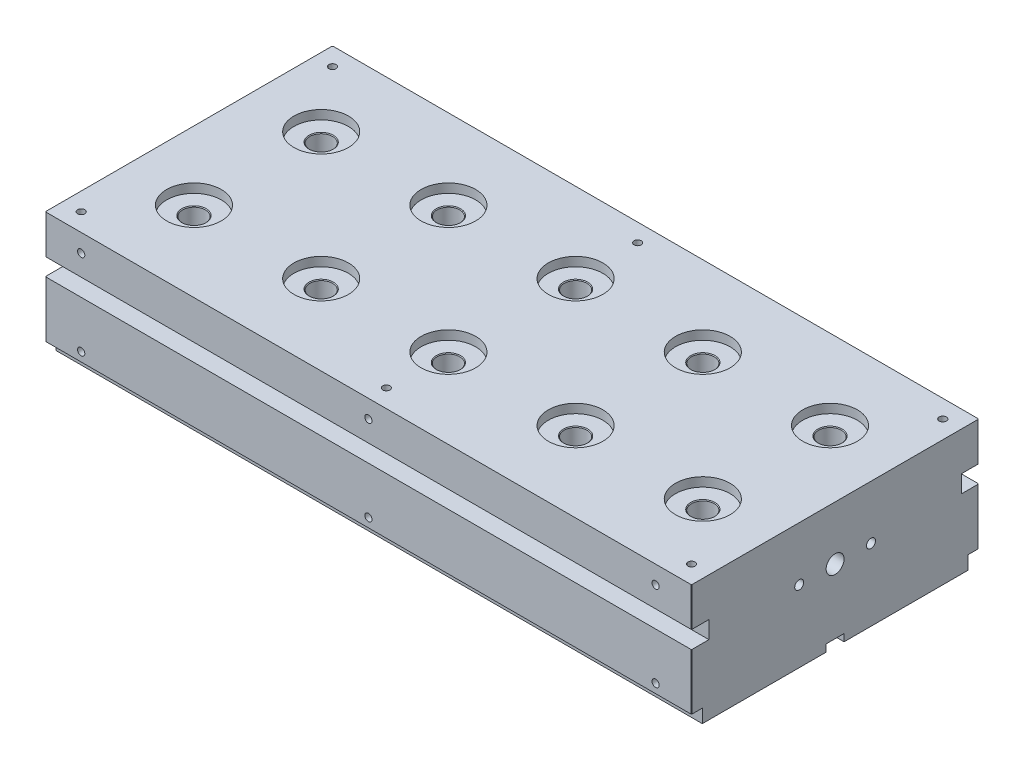
SolidWorks part; units mm, degrees
ref_plane "Front Plane" through (0, 0, 0) normal (0, 0, 1) x (1, 0, 0)
ref_plane "Top Plane" through (0, 0, 0) normal (0, 1, 0) x (1, 0, 0)
ref_plane "Right Plane" through (0, 0, 0) normal (1, 0, 0) x (0, 0, -1)
sketch "Sketch2" plane through (0, 0, 0) normal (0, 1, 0) x (1, 0, 0)
  line L1 (228.6, 101.6) -> (-228.6, 101.6)
  line L2 (228.6, 101.6) -> (228.6, -101.6)
  line L3 (228.6, -101.6) -> (-228.6, -101.6)
  line L4 (-228.6, 101.6) -> (-228.6, -101.6)
  line L5 (0, -101.6) -> (0, 101.6) construction
  line L6 (228.6, 0) -> (-228.6, 0) construction
  point P0 (0, 0)
  dimension "D1" = 457.2
  dimension "D2" = 203.2
extrude "Boss-Extrude1" add sketch "Sketch2" against normal blind 101.6
sketch "Sketch3" plane through (0, 0, 0) normal (0, 1, 0) x (1, 0, 0)
  line L0 (-90, 45) -> (-90, -45) construction
  line L1 (180, 45) -> (-180, 45) construction
  line L2 (180, 45) -> (180, -45) construction
  line L3 (180, -45) -> (-180, -45) construction
  line L4 (-180, 45) -> (-180, -45) construction
  line L5 (0, -45) -> (0, 45) construction
  line L6 (180, 0) -> (-180, 0) construction
  line L7 (90, -45) -> (90, 45) construction
  point P0 (0, 0)
  dimension "D1" = 90
  dimension "D2" = 360
  dimension "D3" = 90
  dimension "D4" = 90
hole_wizard "#97 (0.0059) Diameter Hole1" positions "Sketch4" profile "Sketch5" hole size "#97" standard "ANSI Inch" end condition up to next
sketch "Sketch4" plane through (0, 0, 0) normal (0, 1, 0) x (1, 0, 0)
  point P0 (-180, 45)
  point P3 (-180, -45)
  point P6 (-90, -45)
  point P9 (-90, 45)
  point P12 (0, 45)
  point P15 (0, -45)
  point P18 (90, 45)
  point P21 (90, -45)
  point P24 (180, 45)
  point P27 (180, -45)
sketch "Sketch5" plane through (-180, 0, -45) normal (1, 0, 0) x (0, 0, 1)
  line L0 (0, 0) -> (0, 101.6)
  line L1 (0, 101.6) -> (8.0645, 101.6)
  line L2 (8.0645, 101.6) -> (8.0645, 0)
  line L5 (8.0645, 0) -> (0, 0)
  line L11 (0, -6.35) -> (0, 107.95) construction
  dimension "Thru Hole Dia." = 16.129
  dimension "Thru Hole Depth" = 101.6
sketch "Sketch6" plane through (0, 0, 0) normal (0, 1, 0) x (1, 0, 0)
  circle A0 centre (-180, 45) radius 19.304
  circle A1 centre (-90, 45) radius 19.304
  circle A2 centre (0, 45) radius 19.304
  circle A3 centre (90, 45) radius 19.304
  circle A4 centre (180, 45) radius 19.304
  circle A5 centre (-180, -45) radius 19.304
  circle A6 centre (-90, -45) radius 19.304
  circle A7 centre (0, -45) radius 19.304
  circle A8 centre (90, -45) radius 19.304
  circle A9 centre (180, -45) radius 19.304
  dimension "D1" = 38.608
extrude "Cut-Extrude1" cut sketch "Sketch6" against normal offset from surface (19.1 mm away) 82.5 up to face at (-180, -101.6, -53.0645)
sketch "Sketch7" plane through (228.6, 0, 0) normal (1, 0, 0) x (0, 0, -1)
  line L0 (0, 0) -> (0, -101.6) construction
  line L1 (-101.6, -101.6) -> (101.6, -101.6) construction
  circle A0 centre (0, -50.8) radius 6.35
  dimension "D1" = 12.7
extrude "Cut-Extrude2" cut sketch "Sketch7" against normal through all
sketch "Sketch9" plane through (228.6, 0, 0) normal (1, 0, 0) x (0, 0, -1)
  line L0 (-125.6316, -92.075) -> (-93.96, -92.075)
  line L1 (-93.96, -92.075) -> (-93.96, -105.6328)
  line L2 (-93.96, -105.6328) -> (93.96, -105.6328)
  line L3 (93.96, -105.6328) -> (93.96, -92.075)
  line L4 (93.96, -92.075) -> (107.4884, -92.075)
  line L5 (107.4884, -92.075) -> (107.4884, -145.3143)
  line L6 (107.4884, -145.3143) -> (-125.6316, -145.3143)
  line L7 (-125.6316, -145.3143) -> (-125.6316, -92.075)
  line L8 (-101.6, -101.6) -> (101.6, -101.6) construction
  point P3 (0, -105.6328)
  dimension "D1" = 187.92
  dimension "D2" = 9.525
extrude "Cut-Extrude3" cut sketch "Sketch9" against normal through all
sketch "Sketch10" plane through (0, 0, 93.96) normal (0, 0, 1) x (1, 0, 0)
  line L0 (-228.6, -96.8375) -> (228.6, -96.8375) construction
  line L1 (-228.6, -101.6) -> (-228.6, -92.075) construction
  line L2 (228.6, -101.6) -> (228.6, -92.075) construction
  point P6 (-71.12, -96.8375)
  point P7 (71.12, -96.8375)
  point P8 (-213.36, -96.8375)
  point P9 (213.36, -96.8375)
  dimension "D1" = 71.12
  dimension "D2" = 71.12
  dimension "D3" = 142.24
  dimension "D4" = 142.24
hole_wizard "#4-40 Tapped Hole1" positions "Sketch11" profile "Sketch12" tap size "#4-40" standard "ANSI Inch"
sketch "Sketch11" plane through (0, 0, 93.96) normal (0, 0, 1) x (1, 0, 0)
  point P0 (-213.36, -96.8375)
  point P3 (-71.12, -96.8375)
  point P6 (71.12, -96.8375)
  point P9 (213.36, -96.8375)
sketch "Sketch12" plane through (-213.36, -96.8375, 93.96) normal (1, 0, 0) x (0, -1, 0)
  line L0 (0, 0) -> (0, 9.5692)
  line L1 (0, 9.5692) -> (1.1303, 8.89)
  line L2 (1.1303, 8.89) -> (1.1303, 0.5461)
  line L3 (1.1303, 0.5461) -> (1.6764, 0)
  line L5 (1.6764, 0) -> (0, 0)
  line L6 (-1.1303, 0.5461) -> (-1.6764, 0) construction
  line L10 (0, 9.5692) -> (-1.1303, 8.89) construction
  line L11 (0, -6.35) -> (0, 107.95) construction
  dimension "Tap Drill Dia." = 2.2606
  dimension "Tap Drill Depth" = 8.89
  dimension "Near C'Sink Dia." = 3.3528
  dimension "Near C'Sink Angle" = 90
  dimension "Drill Angle" = 118
cosmetic thread "Hole Thread1" parameters "D1"=5.588, "D2"=2.8448
cosmetic thread "Hole Thread2" parameters "D1"=5.588, "D2"=2.8448
cosmetic thread "Hole Thread3" parameters "D1"=5.588, "D2"=2.8448
cosmetic thread "Hole Thread4" parameters "D1"=5.588, "D2"=2.8448
mirror "Mirror1" about plane through (0, 0, 0) normal (0, 0, 1) of "#4-40 Tapped Hole1"
sketch "Sketch13" plane through (0, -101.6, 0) normal (0, -1, 0) x (1, 0, 0)
  line L0 (238.321, 6.35) -> (-258.7863, 6.35)
  line L1 (-258.7863, -6.35) -> (238.321, -6.35)
  line L2 (238.321, -6.35) -> (238.321, 6.35)
  line L3 (-258.7863, 6.35) -> (-258.7863, -6.35)
  line L4 (-228.6, 0) -> (228.6, 0) construction
  point P2 (238.321, 0)
  dimension "D1" = 12.7
extrude "Cut-Extrude4" cut sketch "Sketch13" against normal blind 5.08
hole_wizard "#10-32 Tapped Hole1" positions "Sketch16" profile "Sketch15" tap size "#10-32" standard "ANSI Inch"
sketch "Sketch16" plane through (0, -96.52, 0) normal (0, -1, 0) x (-1, 0, 0)
  point P0 (0, 0)
sketch "Sketch15" plane through (0, -96.52, 0) normal (1, 0, 0) x (0, 0, -1)
  line L0 (0, 0) -> (0, 14.9293)
  line L1 (0, 14.9293) -> (2.0193, 13.716)
  line L2 (2.0193, 13.716) -> (2.0193, 0.6096)
  line L3 (2.0193, 0.6096) -> (2.6289, 0)
  line L5 (2.6289, 0) -> (0, 0)
  line L6 (-2.0193, 0.6096) -> (-2.6289, 0) construction
  line L10 (0, 14.9293) -> (-2.0193, 13.716) construction
  line L11 (0, -6.35) -> (0, 107.95) construction
  dimension "Tap Drill Dia." = 4.0386
  dimension "Tap Drill Depth" = 13.716
  dimension "Near C'Sink Dia." = 5.2578
  dimension "Near C'Sink Angle" = 90
  dimension "Drill Angle" = 118
cosmetic thread "Hole Thread5" parameters "D1"=9.652, "D2"=4.826
chamfer "Chamfer1" distance 0.508 angle 45 28 edges at (180, 0, -25.696) (180, 0, 64.304) (90, 0, -25.696) (90, 0, 64.304) (0, 0, 64.304) (0, 0, -25.696) (-90, 0, -25.696) (-90, 0, 64.304) (-180, 0, 64.304) (-180, 0, -25.696) (-180, -19.1, -53.0645) (-180, -19.1, 36.9355) (-90, -19.1, 36.9355) (-90, -19.1, -53.0645) (0, -19.1, -53.0645) (0, -19.1, 36.9355) (90, -19.1, -53.0645) (90, -19.1, 36.9355) (180, -19.1, 36.9355) (180, -19.1, -53.0645) (0, 0, -101.6) (228.6, -46.0375, -101.6) (228.6, 0, 0) (228.6, -46.0375, 101.6) (0, 0, 101.6) (-228.6, -46.0375, -101.6) (-228.6, 0, 0) (-228.6, -46.0375, 101.6)
sketch "Sketch17" plane through (-228.6, 0, 0) normal (-1, 0, 0) x (0, 0, 1)
  line L0 (-127.8007, -12.7) -> (122.3798, -12.7)
  line L1 (122.3798, -12.7) -> (122.3798, -40.132)
  line L2 (122.3798, -40.132) -> (89.281, -40.132)
  line L3 (89.281, -40.132) -> (89.281, -52.451)
  line L4 (89.281, -52.451) -> (139.4159, -52.451)
  line L5 (139.4159, -52.451) -> (139.4159, 38.5706)
  line L6 (139.4159, 38.5706) -> (-149.881, 38.5706)
  line L7 (-149.881, 38.5706) -> (-149.881, -52.451)
  line L8 (-149.881, -52.451) -> (-89.281, -52.451)
  line L9 (-89.281, -52.451) -> (-89.281, -40.132)
  line L10 (-89.281, -40.132) -> (-127.8007, -40.132)
  line L11 (-127.8007, -40.132) -> (-127.8007, -12.7)
  line L12 (-101.092, 0) -> (101.092, 0) construction
  line L13 (101.6, -0.508) -> (101.6, -92.075) construction
  line L14 (-101.6, -92.075) -> (-101.6, -0.508) construction
  dimension "D1" = 12.7
  dimension "D2" = 12.319
  dimension "D3" = 12.319
  dimension "D4" = 12.319
  dimension "D5" = 27.432
extrude "Cut-Extrude5" cut sketch "Sketch17" against normal through all both and the other way through all
sketch "Sketch18" plane through (0, -12.7, 0) normal (0, 1, 0) x (1, 0, 0)
  line L0 (228.6, 101.092) -> (228.6, -101.092) construction
  line L1 (215.9, 88.9) -> (-215.9, 88.9) construction
  line L2 (215.9, 88.9) -> (215.9, -88.9) construction
  line L3 (215.9, -88.9) -> (-215.9, -88.9) construction
  line L4 (-215.9, 88.9) -> (-215.9, -88.9) construction
  line L5 (0, -88.9) -> (0, 88.9) construction
  line L6 (215.9, 0) -> (-215.9, 0) construction
  line L7 (-228.092, -101.6) -> (228.092, -101.6) construction
  point P0 (0, 0)
  dimension "D1" = 12.7
  dimension "D2" = 12.7
hole_wizard "1/4-20 Tapped Hole1" positions "Sketch19" profile "Sketch20" tap size "1/4-20" standard "ANSI Inch"
sketch "Sketch19" plane through (0, -12.7, 0) normal (0, 1, 0) x (1, 0, 0)
  point P0 (-215.9, 88.9)
  point P3 (0, 88.9)
  point P6 (215.9, 88.9)
  point P9 (215.9, -88.9)
  point P12 (0, -88.9)
  point P15 (-215.9, -88.9)
sketch "Sketch20" plane through (-215.9, -12.7, -88.9) normal (1, 0, 0) x (0, 0, 1)
  line L0 (0, 0) -> (0, 16.51)
  line L1 (0, 16.51) -> (2.5527, 14.9762)
  line L2 (2.5527, 14.9762) -> (2.5527, 0)
  line L5 (2.5527, 0) -> (0, 0)
  line L10 (0, 16.51) -> (-2.5527, 14.9762) construction
  line L11 (0, -6.35) -> (0, 107.95) construction
  dimension "Tap Drill Dia." = 5.1054
  dimension "Tap Drill Depth" = 16.51
  dimension "Drill Angle" = 118
cosmetic thread "Hole Thread6" parameters "D1"=12.7, "D2"=6.35
cosmetic thread "Hole Thread7" parameters "D1"=12.7, "D2"=6.35
cosmetic thread "Hole Thread8" parameters "D1"=12.7, "D2"=6.35
cosmetic thread "Hole Thread9" parameters "D1"=12.7, "D2"=6.35
cosmetic thread "Hole Thread10" parameters "D1"=12.7, "D2"=6.35
cosmetic thread "Hole Thread11" parameters "D1"=12.7, "D2"=6.35
sketch "Sketch21" plane through (0, 0, 101.6) normal (0, 0, 1) x (1, 0, 0)
  line L0 (0, -101.6) -> (0, -19.608) construction
  line L1 (203.2, -85.725) -> (-203.2, -85.725) construction
  line L2 (203.2, -85.725) -> (203.2, -25.4) construction
  line L3 (203.2, -25.4) -> (-203.2, -25.4) construction
  line L4 (-203.2, -85.725) -> (-203.2, -25.4) construction
  line L5 (0, -25.4) -> (0, -85.725) construction
  line L6 (203.2, -55.5625) -> (-203.2, -55.5625) construction
  line L7 (-228.092, -12.7) -> (228.092, -12.7) construction
  line L8 (228.6, -40.132) -> (228.6, -52.451) construction
  point P0 (0, -55.5625)
  dimension "D1" = 12.7
  dimension "D2" = 25.4
  dimension "D3" = 60.325
hole_wizard "1/4-20 Tapped Hole2" positions "Sketch22" profile "Sketch23" tap size "1/4-20" standard "ANSI Inch"
sketch "Sketch22" plane through (0, 0, 101.6) normal (0, 0, 1) x (1, 0, 0)
  point P0 (-203.2, -25.4)
  point P3 (0, -25.4)
  point P6 (203.2, -25.4)
  point P9 (203.2, -85.725)
  point P12 (0, -85.725)
  point P15 (-203.2, -85.725)
sketch "Sketch23" plane through (-203.2, -25.4, 101.6) normal (1, 0, 0) x (0, -1, 0)
  line L0 (0, 0) -> (0, 16.51)
  line L1 (0, 16.51) -> (2.5527, 14.9762)
  line L2 (2.5527, 14.9762) -> (2.5527, 0)
  line L5 (2.5527, 0) -> (0, 0)
  line L10 (0, 16.51) -> (-2.5527, 14.9762) construction
  line L11 (0, -6.35) -> (0, 107.95) construction
  dimension "Tap Drill Dia." = 5.1054
  dimension "Tap Drill Depth" = 16.51
  dimension "Drill Angle" = 118
cosmetic thread "Hole Thread12" parameters "D1"=12.7, "D2"=6.35
cosmetic thread "Hole Thread13" parameters "D1"=12.7, "D2"=6.35
cosmetic thread "Hole Thread14" parameters "D1"=12.7, "D2"=6.35
cosmetic thread "Hole Thread15" parameters "D1"=12.7, "D2"=6.35
cosmetic thread "Hole Thread16" parameters "D1"=12.7, "D2"=6.35
cosmetic thread "Hole Thread17" parameters "D1"=12.7, "D2"=6.35
mirror "Mirror2" about plane through (0, 0, 0) normal (0, 0, 1) of "1/4-20 Tapped Hole2"
sketch "Sketch24" plane through (228.6, 0, 0) normal (1, 0, 0) x (0, 0, -1)
  line L0 (-25.4, -50.8) -> (25.4, -50.8) construction
  circle A0 centre (0, -50.8) radius 6.35 construction
  circle A1 centre (-25.4, -50.8) radius 3.175
  circle A2 centre (25.4, -50.8) radius 3.175
  point P4 (0, -50.8)
  dimension "D2" = 6.35
  dimension "D1" = 50.8
hole_wizard "1/4 (0.25) Diameter Hole1" positions "Sketch25" profile "Sketch26" hole size "1/4" standard "ANSI Inch"
sketch "Sketch25" plane through (228.6, 0, 0) normal (1, 0, 0) x (0, 0, -1)
  point P0 (-25.4, -50.8)
  point P3 (25.4, -50.8)
sketch "Sketch26" plane through (228.6, -50.8, 25.4) normal (0, 1, 0) x (0, 0, -1)
  line L0 (0, 0) -> (0, 37.4677)
  line L1 (0, 37.4677) -> (3.175, 35.56)
  line L2 (3.175, 35.56) -> (3.175, 0)
  line L5 (3.175, 0) -> (0, 0)
  line L10 (0, 37.4677) -> (-3.175, 35.56) construction
  line L11 (0, -6.35) -> (0, 107.95) construction
  dimension "Hole Dia." = 6.35
  dimension "Hole Depth" = 35.56
  dimension "Drill Angle" = 118
equation "\"D3@Sketch10\"=\"D1@Sketch10\"*2"
equation "\"D4@Sketch10\"=\"D1@Sketch10\"*2"
